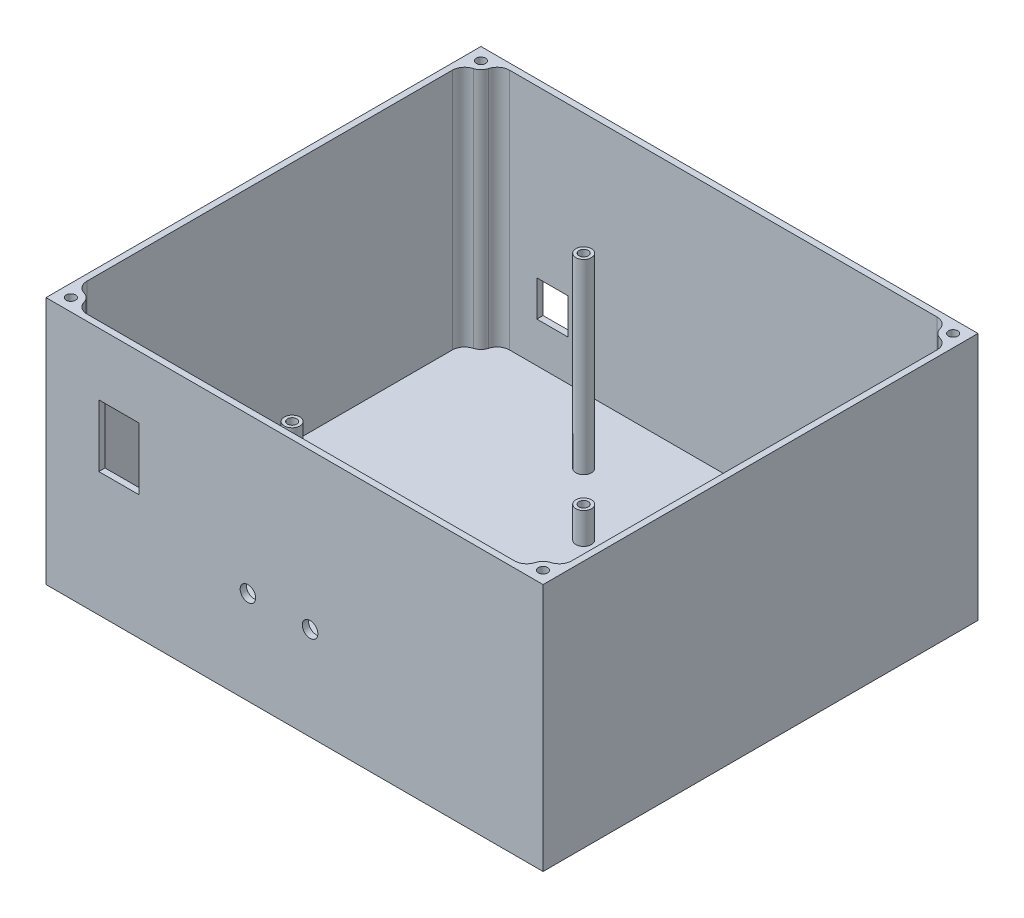
SolidWorks part; units mm, degrees
ref_plane "Front Plane" through (0, 0, 0) normal (0, 0, 1) x (1, 0, 0)
ref_plane "Top Plane" through (0, 0, 0) normal (0, 1, 0) x (1, 0, 0)
ref_plane "Right Plane" through (0, 0, 0) normal (1, 0, 0) x (0, 0, -1)
sketch "Sketch1" plane through (0, 0, 0) normal (0, 1, 0) x (1, 0, 0)
  line L1 (-80, 70) -> (80, 70)
  line L2 (-80, 70) -> (-80, -70)
  line L3 (-80, -70) -> (80, -70)
  line L4 (80, 70) -> (80, -70)
  line L5 (-80, 70) -> (80, -70) construction
  line L6 (-80, -70) -> (80, 70) construction
  point P0 (0, 0)
  dimension "D1" = 160
  dimension "D2" = 140
extrude "Boss-Extrude1" add sketch "Sketch1" along normal blind 80
sketch "Sketch2" plane through (0, 80, 0) normal (0, 1, 0) x (1, 0, 0)
  line L0 (80, 70) -> (-80, 70) construction
  line L1 (-80, 70) -> (-80, -70) construction
  line L2 (80, -70) -> (80, 70) construction
  line L3 (-80, -70) -> (80, -70) construction
  point P0 (-76, 66)
  point P1 (76, 66)
  point P2 (76, -66)
  point P3 (-76, -66)
  dimension "D1" = 4
  dimension "D2" = 4
  dimension "D3" = 4
  dimension "D4" = 4
hole_wizard "Ø3.0mm Dowel Hole3" positions "Sketch7" profile "Sketch8" hole size "Ø3.0" standard "ANSI Metric" end condition through all
sketch "Sketch7" plane through (0, 80, 0) normal (0, 1, 0) x (1, 0, 0)
  point P0 (-76, 66)
  point P3 (76, 66)
  point P6 (76, -66)
  point P9 (-76, -66)
sketch "Sketch8" plane through (-76, 80, -66) normal (1, 0, 0) x (0, 0, 1)
  line L0 (0, 0) -> (0, 80)
  line L1 (0, 80) -> (1.5, 80)
  line L2 (1.5, 80) -> (1.5, 0)
  line L5 (1.5, 0) -> (0, 0)
  line L11 (0, -6.35) -> (0, 107.95) construction
  dimension "Thru Hole Dia." = 3
  dimension "Thru Hole Depth" = 80
shell "Shell1" thickness 2
sketch "Sketch10" plane through (0, 2, 0) normal (0, 1, 0) x (1, 0, 0)
  line L0 (80, -70) -> (80, 70) construction
  line L1 (80, 70) -> (-80, 70) construction
  circle A0 centre (70, 46.925) radius 2.5
  circle A1 centre (-23.85, 46.925) radius 2.5
  circle A2 centre (-23.85, -46.925) radius 2.5
  circle A3 centre (70, -46.925) radius 2.5
  dimension "D3" = 5
  dimension "D5" = 5
  dimension "D7" = 5
  dimension "D8" = 5
  dimension "D1" = 10
  dimension "D2" = 23.075
  dimension "D4" = 93.85
  dimension "D6" = 93.85
extrude "Boss-Extrude3" add sketch "Sketch10" along normal blind 60
hole_wizard "Ø3.0mm Dowel Hole2" positions "Sketch13" profile "Sketch14" hole size "Ø3.0" standard "ANSI Metric"
sketch "Sketch13" plane through (0, 62, 0) normal (0, 1, 0) x (1, 0, 0)
  point P0 (-23.85, 46.925)
  point P3 (70, 46.925)
  point P6 (70, -46.925)
  point P9 (-23.85, -46.925)
sketch "Sketch14" plane through (-23.85, 62, -46.925) normal (1, 0, 0) x (0, 0, 1)
  line L0 (0, 0) -> (0, 45.9013)
  line L1 (0, 45.9013) -> (1.5, 45)
  line L2 (1.5, 45) -> (1.5, 0)
  line L5 (1.5, 0) -> (0, 0)
  line L10 (0, 45.9013) -> (-1.5, 45) construction
  line L11 (0, -6.35) -> (0, 107.95) construction
  dimension "Hole Dia." = 3
  dimension "Hole Depth" = 45
  dimension "Drill Angle" = 118
fillet "Fillet1" radius 4 8 edges at (78, 41, 63.1277) (73.1277, 41, 68) (-78, 41, 63.1277) (-73.1277, 41, 68) (78, 41, -63.1277) (73.1277, 41, -68) (-73.1277, 41, -68) (-78, 41, -63.1277)
sketch "Sketch15" plane through (0, 2, 0) normal (0, 1, 0) x (1, 0, 0)
  line L2 (80, -70) -> (80, 70) construction
  line L3 (80, 70) -> (-80, 70) construction
  circle A0 centre (-3.85, 26.925) radius 2.5
  circle A1 centre (50, 26.925) radius 2.5
  circle A2 centre (-3.85, -26.925) radius 2.5
  circle A3 centre (50, -26.925) radius 2.5
  dimension "D5" = 5
  dimension "D6" = 5
  dimension "D7" = 5
  dimension "D8" = 5
  dimension "D1" = 53.85
  dimension "D2" = 30
  dimension "D3" = 53.85
  dimension "D10" = 43.075
extrude "Boss-Extrude5" add sketch "Sketch15" along normal blind 10
hole_wizard "Ø3.0mm Dowel Hole5" positions "Sketch18" profile "Sketch19" hole size "Ø3.0" standard "ANSI Metric" end condition through all
sketch "Sketch18" plane through (0, 12, 0) normal (0, 1, 0) x (1, 0, 0)
  point P0 (-3.85, 26.925)
  point P3 (50, 26.925)
  point P6 (50, -26.925)
  point P9 (-3.85, -26.925)
sketch "Sketch19" plane through (-3.85, 12, -26.925) normal (1, 0, 0) x (0, 0, 1)
  line L0 (0, 0) -> (0, 12)
  line L1 (0, 12) -> (1.5, 12)
  line L2 (1.5, 12) -> (1.5, 0)
  line L5 (1.5, 0) -> (0, 0)
  line L11 (0, -6.35) -> (0, 107.95) construction
  dimension "Thru Hole Dia." = 3
  dimension "Thru Hole Depth" = 12
sketch "Sketch20" plane through (0, 0, 70) normal (0, 0, 1) x (1, 0, 0)
  line L0 (-80, 80) -> (80, 80) construction
  line L1 (-63, 60) -> (-50, 60)
  line L2 (-63, 60) -> (-63, 40)
  line L3 (-63, 40) -> (-50, 40)
  line L4 (-50, 60) -> (-50, 40)
  line L5 (-63, 60) -> (-50, 40) construction
  line L6 (-63, 40) -> (-50, 60) construction
  line L7 (80, 80) -> (80, 0) construction
  point P0 (-56.5, 50)
  dimension "D1" = 20
  dimension "D2" = 13
  dimension "D3" = 20
  dimension "D4" = 130
extrude "Cut-Extrude1" cut sketch "Sketch20" against normal blind 2
sketch "Sketch24" plane through (0, 0, 70) normal (0, 0, 1) x (1, 0, 0)
  line L0 (-80, 0) -> (80, 0) construction
  line L1 (80, 80) -> (80, 0) construction
  point P0 (-15, 30)
  point P1 (5, 30)
  dimension "D1" = 30
  dimension "D2" = 20
  dimension "D3" = 75
hole_wizard "Ø5.0mm Dowel Hole1" positions "Sketch25" profile "Sketch26" hole size "Ø5.0" standard "ANSI Metric" end condition up to next
sketch "Sketch25" plane through (0, 0, 70) normal (0, 0, 1) x (1, 0, 0)
  point P0 (-15, 30)
  point P3 (5, 30)
sketch "Sketch26" plane through (-15, 30, 70) normal (1, 0, 0) x (0, -1, 0)
  line L0 (0, 0) -> (0, 2)
  line L1 (0, 2) -> (2.5, 2)
  line L2 (2.5, 2) -> (2.5, 0)
  line L5 (2.5, 0) -> (0, 0)
  line L11 (0, -6.35) -> (0, 107.95) construction
  dimension "Thru Hole Dia." = 5
  dimension "Thru Hole Depth" = 2
sketch "Sketch27" plane through (0, 0, -70) normal (0, 0, -1) x (-1, 0, 0)
  line L0 (-80, 0) -> (80, 0) construction
  line L1 (50, 26.5) -> (60, 26.5)
  line L2 (50, 26.5) -> (50, 15)
  line L3 (50, 15) -> (60, 15)
  line L4 (60, 26.5) -> (60, 15)
  line L5 (50, 26.5) -> (60, 15) construction
  line L6 (50, 15) -> (60, 26.5) construction
  line L7 (80, 80) -> (80, 0) construction
  point P0 (55, 20.75)
  dimension "D1" = 10
  dimension "D2" = 11.5
  dimension "D3" = 15
  dimension "D4" = 30
extrude "Cut-Extrude2" cut sketch "Sketch27" against normal blind 2
